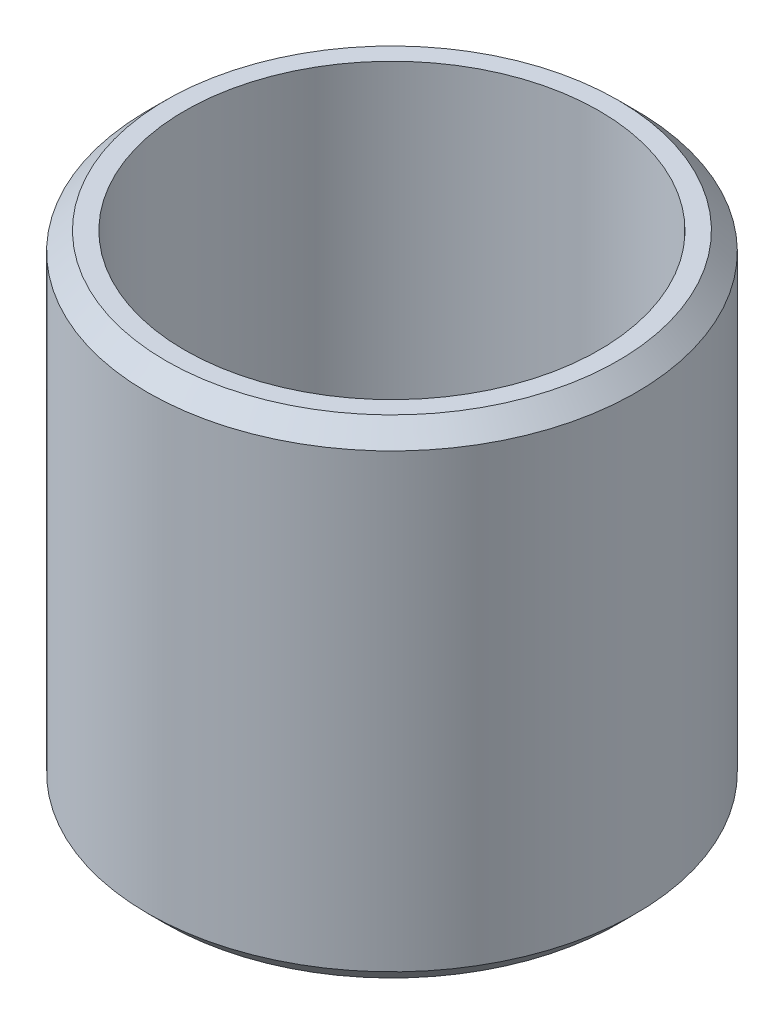
SolidWorks part; units mm, degrees
ref_plane "Front Plane" through (0, 0, 0) normal (0, 0, 1) x (1, 0, 0)
ref_plane "Top Plane" through (0, 0, 0) normal (0, 1, 0) x (1, 0, 0)
ref_plane "Right Plane" through (0, 0, 0) normal (1, 0, 0) x (0, 0, -1)
sketch "Sketch1" plane through (0, 0, 0) normal (0, 1, 0) x (1, 0, 0)
  circle A0 centre (0, 0) radius 17
  circle A1 centre (0, 0) radius 20.032
  dimension "D1" = 40.064
  dimension "D2" = 34
extrude "Extrude1" add sketch "Sketch1" along normal mid plane 40
chamfer "Bushing Chamfer" distance 1.5 distance2 1.5 2 edges at (0, 20, 20.032) (0, -20, 20.032)
